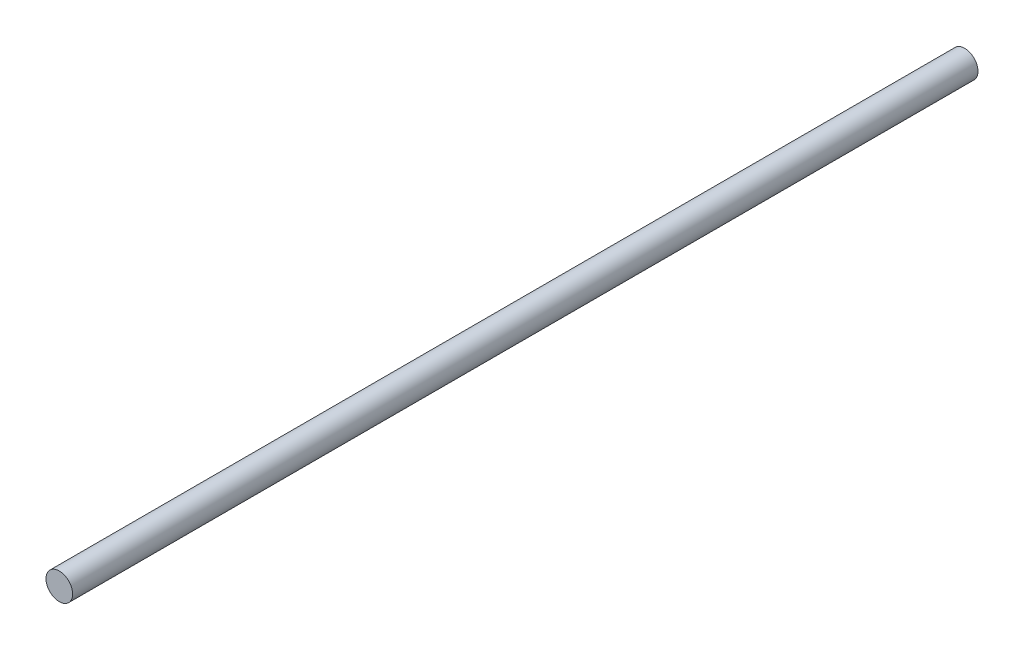
SolidWorks part; units mm, degrees
ref_plane "Front Plane" through (0, 0, 0) normal (0, 0, 1) x (1, 0, 0)
ref_plane "Top Plane" through (0, 0, 0) normal (0, 1, 0) x (1, 0, 0)
ref_plane "Right Plane" through (0, 0, 0) normal (1, 0, 0) x (0, 0, -1)
sketch "Sketch1" plane through (0, 0, 0) normal (0, 0, 1) x (1, 0, 0)
  circle A0 centre (0, 0) radius 0.5
extrude "Boss-Extrude1" add sketch "Sketch1" along normal blind 34
